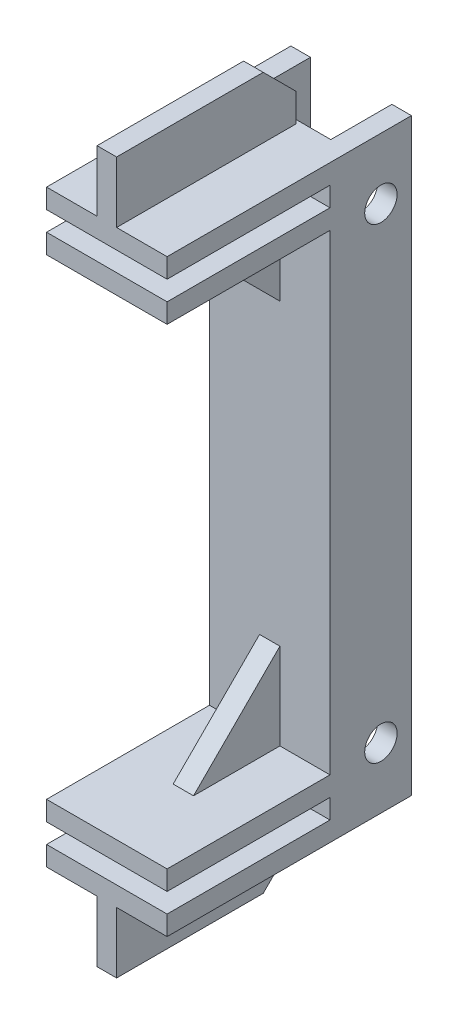
SolidWorks part; units mm, degrees
material "Titanium Ti-5Al-2.5Sn"
ref_plane "Front Plane" through (0, 0, 0) normal (0, 0, 1) x (1, 0, 0)
ref_plane "Top Plane" through (0, 0, 0) normal (0, 1, 0) x (1, 0, 0)
ref_plane "Right Plane" through (0, 0, 0) normal (1, 0, 0) x (0, 0, -1)
sketch "Sketch1" plane through (0, 0, 0) normal (1, 0, 0) x (0, 0, -1)
  line L0 (-18.5097, 0) -> (22.7026, 0) construction
  line L1 (-6.35, -45.9105) -> (6.35, -45.9105)
  line L2 (-6.35, -36.7665) -> (-6.35, 36.7665)
  line L3 (-6.35, 45.9105) -> (6.35, 45.9105)
  line L4 (6.35, -45.9105) -> (6.35, 45.9105)
  line L5 (-6.35, -45.9105) -> (6.35, 45.9105) construction
  line L6 (-6.35, 45.9105) -> (6.35, -45.9105) construction
  line L7 (-6.35, 45.9105) -> (-31.75, 45.9105)
  line L9 (-6.35, 36.7665) -> (-31.75, 36.7665)
  line L10 (-31.75, 45.9105) -> (-31.75, 42.8625)
  line L11 (-31.75, 39.8145) -> (-31.75, 36.7665)
  line L12 (-31.75, 42.8625) -> (-6.35, 42.8625)
  line L14 (-31.75, 39.8145) -> (-6.35, 39.8145)
  line L15 (-6.35, 42.8625) -> (-6.35, 39.8145)
  line L16 (-6.35, -42.8625) -> (-6.35, -39.8145)
  line L17 (-31.75, -39.8145) -> (-6.35, -39.8145)
  line L18 (-31.75, -42.8625) -> (-6.35, -42.8625)
  line L19 (-31.75, -39.8145) -> (-31.75, -36.7665)
  line L20 (-31.75, -45.9105) -> (-31.75, -42.8625)
  line L21 (-6.35, -36.7665) -> (-31.75, -36.7665)
  line L22 (-6.35, -45.9105) -> (-31.75, -45.9105)
  circle A0 centre (1.5875, 36.3855) radius 2.5273
  circle A1 centre (1.5875, -36.3855) radius 2.5273
  point P0 (0, 0)
  point P24 (0, 45.9105)
  point P25 (0, 0)
  point P27 (6.35, 35.9582)
  point P29 (0.8764, 45.9105)
  dimension "D8" = 5.0546
  dimension "D1" = 91.821
  dimension "D2" = 12.7
  dimension "D3" = 9.144
  dimension "D4" = 25.4
  dimension "D5" = 3.048
  dimension "D6" = 3.048
  dimension "D7" = 25.4
  dimension "D9" = 4.7625
  dimension "D10" = 9.525
extrude "Boss-Extrude2" add sketch "Sketch1" along normal mid plane 18.796
sketch "Sketch2" plane through (0, 0, 0) normal (1, 0, 0) x (0, 0, -1)
  line L0 (-8.89, 55.4355) -> (-3.81, 50.3555)
  line L1 (-31.75, 45.9105) -> (-3.81, 45.9105)
  line L2 (-31.75, 45.9105) -> (-31.75, 55.4355)
  line L3 (-31.75, 55.4355) -> (-8.89, 55.4355)
  line L4 (-3.81, 45.9105) -> (-3.81, 50.3555)
  line L5 (0, 0) -> (-31.75, 0) construction
  line L6 (-31.75, -45.9105) -> (-31.75, -55.4355)
  line L7 (-31.75, -55.4355) -> (-8.89, -55.4355)
  line L8 (-8.89, -55.4355) -> (-3.81, -50.3555)
  line L9 (-3.81, -45.9105) -> (-3.81, -50.3555)
  line L10 (-31.75, -45.9105) -> (-3.81, -45.9105)
  dimension "D1" = 27.94
  dimension "D2" = 9.525
  dimension "D3" = 22.86
  dimension "D4" = 135
extrude "Boss-Extrude3" add sketch "Sketch2" along normal mid plane 3.048
sketch "Sketch3" plane through (0, 0, 0) normal (1, 0, 0) x (0, 0, -1)
  line L0 (-19.8204, 36.7665) -> (-6.35, 23.2961)
  line L3 (-31.75, 36.7665) -> (-6.35, 36.7665) construction
  line L4 (-6.35, 36.7665) -> (-6.35, -36.7665) construction
  line L5 (-19.8204, 36.7665) -> (-6.35, 36.7665)
  line L6 (-6.35, 36.7665) -> (-6.35, 23.2961)
  line L7 (-12.8858, 0) -> (19.6445, 0) construction
  line L8 (-19.8204, -36.7665) -> (-6.35, -36.7665)
  line L9 (-19.8204, -36.7665) -> (-6.35, -23.2961)
  line L10 (-6.35, -36.7665) -> (-6.35, -23.2961)
  dimension "D1" = 19.05
  dimension "D2" = 45
extrude "Boss-Extrude4" add sketch "Sketch3" along normal mid plane 3.175
sketch "Sketch4" plane through (0, 0, 0) normal (0, 1, 0) x (1, 0, 0)
  line L0 (9.398, 6.35) -> (-9.398, 6.35) construction
  line L1 (-6.35, 6.35) -> (6.35, 6.35)
  line L2 (-6.35, 6.35) -> (-6.35, -3.175)
  line L3 (-6.35, -3.175) -> (6.35, -3.175)
  line L4 (6.35, 6.35) -> (6.35, -3.175)
  dimension "D1" = 12.7
  dimension "D2" = 9.525
  dimension "D3" = 3.048
extrude "Cut-Extrude1" cut sketch "Sketch4" against normal through all both and the other way through all contours L2 L1 L4 L3
